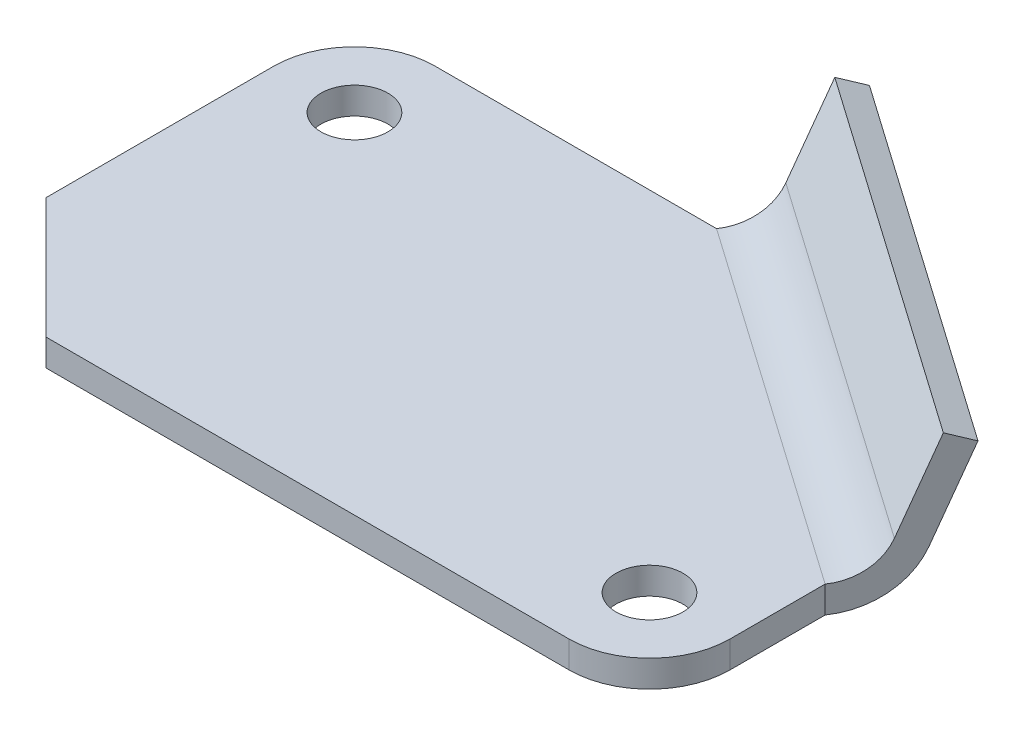
SolidWorks part; units mm, degrees
ref_plane "Front Plane" through (0, 0, 0) normal (0, 0, 1) x (1, 0, 0)
ref_plane "Top Plane" through (0, 0, 0) normal (0, 1, 0) x (1, 0, 0)
ref_plane "Right Plane" through (0, 0, 0) normal (1, 0, 0) x (0, 0, -1)
sketch "Sketch1" plane through (0, 0, 0) normal (0, 1, 0) x (1, 0, 0)
  line L0 (-54, -14) -> (-36, -32)
  line L1 (-36, -32) -> (42, -32)
  line L2 (-54, -14) -> (-54, 20)
  line L3 (-42, 32) -> (0, 32)
  line L4 (54, -20) -> (54, -5.8112)
  line L5 (-54, -32) -> (24.7525, 14.6681) construction
  line L6 (-54, 32) -> (54, -32) construction
  line L7 (0, 32) -> (54, -5.8112)
  arc A0 (-54, 20) -> (-42, 32) centre (-42, 20) cw
  arc A1 (42, -32) -> (54, -20) centre (42, -20) ccw
  circle A2 centre (-42, 20) radius 5
  circle A3 centre (42, -20) radius 5
  point P0 (0, 0)
  dimension "D3" = 12
  dimension "D6" = 10
  dimension "D1" = 108
  dimension "D2" = 64
  dimension "D4" = 35
  dimension "D5" = 54
extrude "Boss-Extrude1" add sketch "Sketch1" along normal blind 4
ref_plane "Plane1" through (38.9649, 0, 27.2835) normal (0.8192, 0, 0.5736) x (0, -1, 0)
sketch "Sketch2" plane through (38.9649, 0, 27.2835) normal (0.8192, 0, 0.5736) x (0, -1, 0)
  line L0 (-9.0031, 33.6303) -> (-21.9837, 38.8748)
  line L6 (-7.5047, 37.3391) -> (-20.4853, 42.5836)
  line L7 (-4, 14.5901) -> (-4, 26.2129) construction
  line L8 (0, 26.2129) -> (-4, 26.2129)
  line L9 (-20.4853, 42.5836) -> (-21.9837, 38.8748)
  line L10 (-4, 26.2129) -> (0, 26.2129) construction
  arc A0 (0, 26.2129) -> (-7.5047, 37.3391) centre (-12, 26.2129) ccw
  arc A1 (-4, 26.2129) -> (-9.0031, 33.6303) centre (-12, 26.2129) ccw
  dimension "D1" = 24
  dimension "D2" = 112
  dimension "D4" = 14
  dimension "D3" = 4
extrude "Boss-Extrude2" add sketch "Sketch2" against normal up to vertex (65.9218 mm away)
